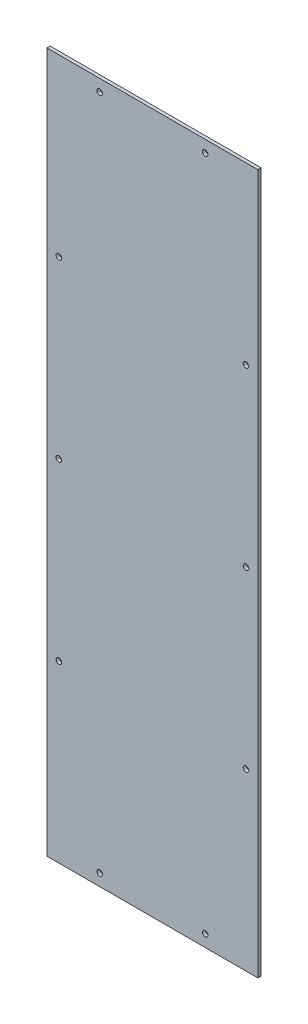
SolidWorks part; units mm, degrees
ref_plane "Front Plane" through (0, 0, 0) normal (0, 0, 1) x (1, 0, 0)
ref_plane "Top Plane" through (0, 0, 0) normal (0, 1, 0) x (1, 0, 0)
ref_plane "Right Plane" through (0, 0, 0) normal (1, 0, 0) x (0, 0, -1)
sketch "Sketch1" plane through (0, 0, 0) normal (0, 0, 1) x (1, 0, 0)
  line L0 (0, 474.9458) -> (0, -405.0542) construction
  line L1 (-391.5523, 474.9458) -> (-126.2723, 474.9458)
  line L2 (-126.2723, 474.9458) -> (-126.2723, -405.0542)
  line L3 (-126.2723, -405.0542) -> (-391.5523, -405.0542)
  line L4 (-391.5523, -405.0542) -> (-391.5523, 474.9458)
  dimension "D1" = 880
  dimension "D2" = 265.28
extrude "Boss-Extrude1" add sketch "Sketch1" along normal blind 4
sketch "Sketch2" plane through (0, 0, 4) normal (0, 0, 1) x (1, 0, 0)
  line L0 (-376.5523, 517.2059) -> (-376.5523, -475.1369) construction
  line L1 (-391.5523, 474.9458) -> (-391.5523, -405.0542) construction
  line L2 (-421.8429, 459.9458) -> (-84.5794, 459.9458) construction
  line L3 (-126.2723, 474.9458) -> (-391.5523, 474.9458) construction
  line L4 (-141.2723, 517.2059) -> (-141.2723, -461.3398) construction
  line L5 (-421.8429, -390.0542) -> (-84.5794, -390.0542) construction
  line L6 (-391.5523, -405.0542) -> (-126.2723, -405.0542) construction
  line L7 (-126.2723, -405.0542) -> (-126.2723, 474.9458) construction
  circle A0 centre (-325.2323, 459.9458) radius 3.5
  circle A1 centre (-192.5923, 459.9458) radius 3.5
  circle A2 centre (-325.2323, -390.0542) radius 3.5
  circle A3 centre (-192.5923, -390.0542) radius 3.5
  circle A4 centre (-376.5523, 254.9458) radius 3.5
  circle A5 centre (-376.5523, -185.0542) radius 3.5
  circle A6 centre (-141.2723, -185.0542) radius 3.5
  circle A7 centre (-141.2723, 254.9458) radius 3.5
  circle A8 centre (-376.5523, 34.9458) radius 3.5
  circle A9 centre (-141.2723, 34.9458) radius 3.5
  dimension "D6" = 7
  dimension "D1" = 15
  dimension "D2" = 15
  dimension "D3" = 15
  dimension "D4" = 15
  dimension "D5" = 220
  dimension "D7" = 220
  dimension "D8" = 440
  dimension "D9" = 66.32
  dimension "D10" = 66.32
extrude "Cut-Extrude1" cut sketch "Sketch2" against normal blind 4
ref_point "Point1"
